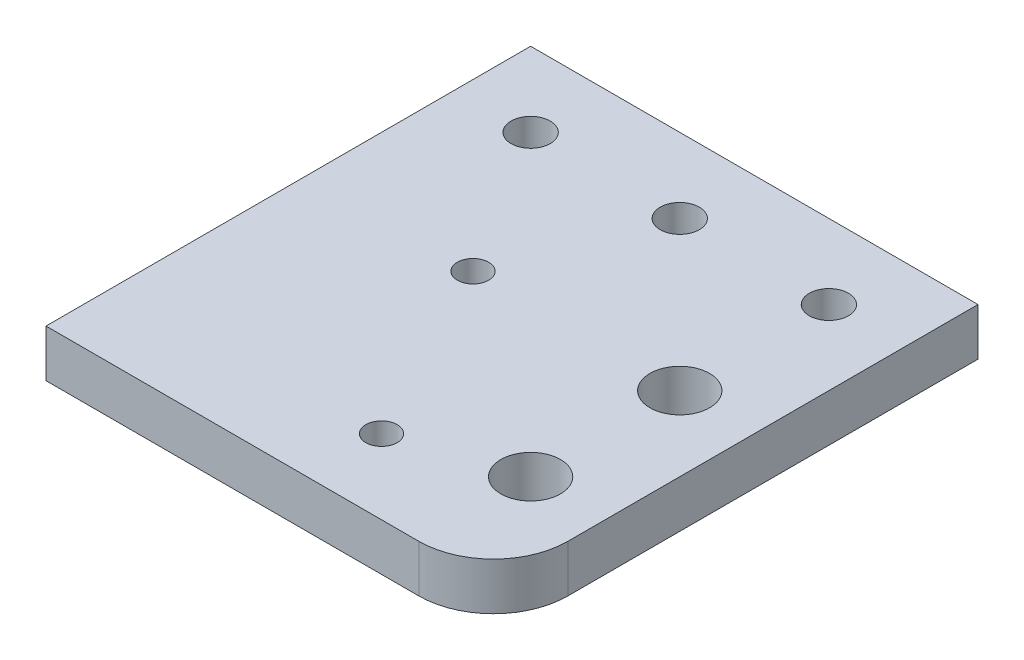
SolidWorks part; units mm, degrees
ref_plane "Front Plane" through (0, 0, 0) normal (0, 0, 1) x (1, 0, 0)
ref_plane "Top Plane" through (0, 0, 0) normal (0, 1, 0) x (1, 0, 0)
ref_plane "Right Plane" through (0, 0, 0) normal (1, 0, 0) x (0, 0, -1)
sketch "Sketch1" plane through (0, 0, 0) normal (0, 1, 0) x (1, 0, 0)
  line L0 (0, -10) -> (60, -10) construction
  line L1 (0, 0) -> (60, 0)
  line L2 (0, 0) -> (0, -65)
  line L3 (0, -65) -> (60, -65)
  line L4 (60, 0) -> (60, -65)
  line L5 (22.27, -30) -> (35, -55) construction
  circle A0 centre (10, -10) radius 2.625
  circle A1 centre (30, -10) radius 2.625
  circle A2 centre (50, -10) radius 2.625
  circle A3 centre (22.27, -30) radius 2.1
  circle A4 centre (35, -55) radius 2.1
  dimension "D4" = 5.25
  dimension "D5" = 10
  dimension "D8" = 5.25
  dimension "D12" = 4.2
  dimension "D1" = 10
  dimension "D2" = 60
  dimension "D3" = 65
  dimension "D6" = 20
  dimension "D7" = 20
  dimension "D9" = 25
  dimension "D10" = 25
  dimension "D11" = 12.73
  dimension "D13" = 20
extrude "Boss-Extrude1" add sketch "Sketch1" along normal blind 6.35
fillet "Fillet1" radius 10 1 edges at (60, 3.175, 65)
sketch "Sketch2" plane through (0, 6.35, 0) normal (0, 1, 0) x (1, 0, 0)
  line L0 (50, -10) -> (50, -65) construction
  line L1 (0, -65) -> (50, -65) construction
  circle A0 centre (50, -30) radius 4
  circle A1 centre (50, -50) radius 4
  dimension "D4" = 8
  dimension "D1" = 20
  dimension "D2" = 40
extrude "Cut-Extrude1" cut sketch "Sketch2" against normal through all
